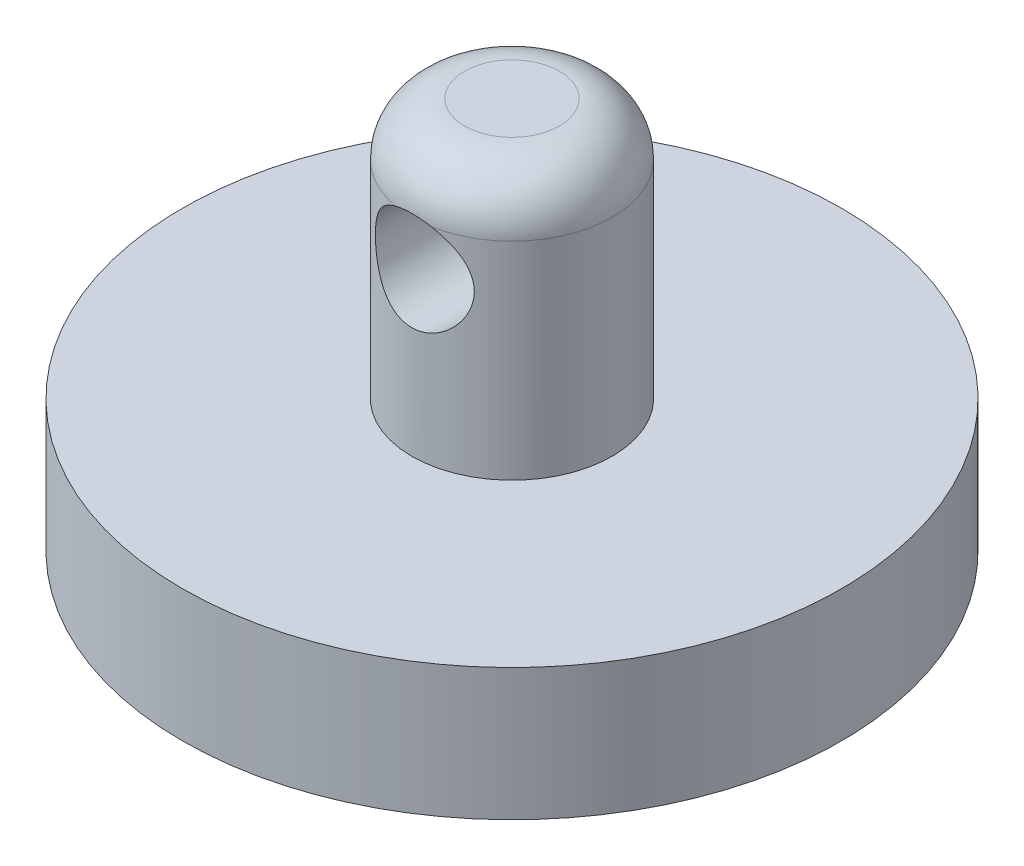
SolidWorks part; units mm, degrees
ref_plane "Front Plane" through (0, 0, 0) normal (0, 0, 1) x (1, 0, 0)
ref_plane "Top Plane" through (0, 0, 0) normal (0, 1, 0) x (1, 0, 0)
ref_plane "Right Plane" through (0, 0, 0) normal (1, 0, 0) x (0, 0, -1)
sketch "Sketch1" plane through (0, 0, 0) normal (0, 0, 1) x (1, 0, 0)
  line L0 (0, 0) -> (2.286, 0)
  line L1 (4.826, -2.54) -> (4.826, -12.5095)
  line L2 (4.826, -12.5095) -> (15.875, -12.5095)
  line L3 (15.875, -12.5095) -> (15.875, -18.8595)
  line L4 (15.875, -18.8595) -> (12.7, -18.8595)
  line L5 (12.7, -18.8595) -> (12.7, -15.6845)
  line L6 (12.7, -15.6845) -> (0, -15.6845)
  line L9 (0, 0) -> (0, -15.6845)
  line L10 (0, 0) -> (0, -36.8992) construction
  arc A0 (2.286, 0) -> (4.826, -2.54) centre (2.286, -2.54) cw
  point P12 (4.826, 0)
  point P13 (1.143, 0)
  dimension "D5" = 2.54
  dimension "D1" = 12.7
  dimension "D2" = 3.175
  dimension "D3" = 3.175
  dimension "D4" = 3.175
  dimension "D6" = 4.826
  dimension "D7" = 15.6845
revolve "Revolve1" add sketch "Sketch1" angle 360 about L10
sketch "Sketch2" plane through (0, 0, 0) normal (0, 1, 0) x (1, 0, 0)
  line L0 (0, 0) -> (0, -4.826) construction
  circle A0 centre (0, 0) radius 4.826 construction
ref_plane "Plane1" through (0, 0, 4.826) normal (0, 0, 1) x (1, 0, 0)
sketch "Sketch3" plane through (0, 0, 4.826) normal (0, 0, 1) x (1, 0, 0)
  line L0 (0, 0) -> (0, -10.5129) construction
  line L1 (2.286, 0) -> (-2.286, 0) construction
  line L2 (-15.875, -18.8595) -> (15.875, -18.8595) construction
  circle A0 centre (0, -4.7625) radius 2.3813
  dimension "D1" = 4.7625
  dimension "D2" = 14.097
extrude "Cut-Extrude1" cut sketch "Sketch3" against normal blind 19.0451
